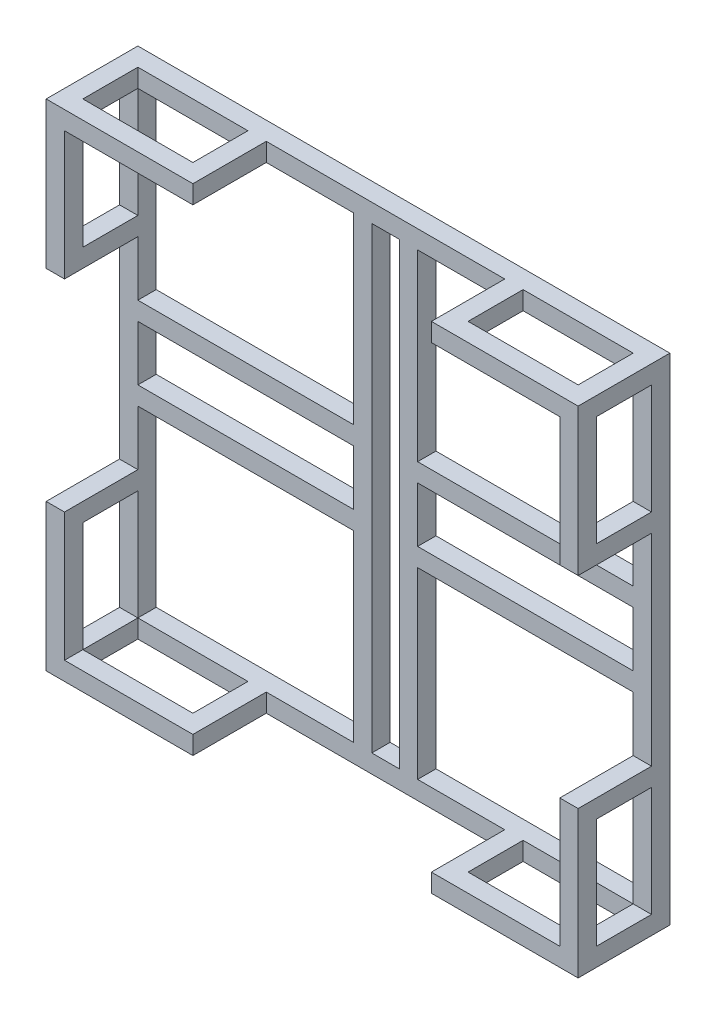
SolidWorks part; units mm, degrees
ref_plane "前视基准面" through (0, 0, 0) normal (0, 0, 1) x (1, 0, 0)
ref_plane "上视基准面" through (0, 0, 0) normal (0, 1, 0) x (1, 0, 0)
ref_plane "右视基准面" through (0, 0, 0) normal (1, 0, 0) x (0, 0, -1)
sketch "草图1" plane through (0, 0, 0) normal (0, 0, 1) x (1, 0, 0)
  line L1 (0, 0) -> (580, 0)
  line L2 (0, 0) -> (0, 540)
  line L3 (0, 540) -> (580, 540)
  line L4 (580, 0) -> (580, 540)
  dimension "D1" = 580
  dimension "D2" = 540
extrude "凸台-拉伸1" add sketch "草图1" along normal blind 100 contours L3 L4 L1 L2
shell "抽壳1" thickness 20
sketch "草图2" plane through (0, 0, 20) normal (0, 0, 1) x (1, 0, 0)
  line L1 (560, 20) -> (325, 20)
  line L2 (560, 20) -> (560, 220)
  line L3 (560, 220) -> (325, 220)
  line L4 (325, 20) -> (325, 220)
  dimension "D1" = 235
  dimension "D2" = 200
extrude "切除-拉伸1" cut sketch "草图2" against normal blind 43 contours L3 L4 L1 L2
pattern_linear "阵列(线性)1" count 2 spacing 305 along (-1, 0, 0) of "切除-拉伸1"
pattern_linear "阵列(线性)2" count 2 spacing 300 along (0, 1, 0) of "切除-拉伸1"
pattern_linear "阵列(线性)3" count 2 spacing 300 along (0, 1, 0) of "阵列(线性)1"
sketch "草图3" plane through (0, 0, 0) normal (0, -1, 0) x (1, 0, 0)
  line L0 (580, 100) -> (420, 100) construction
  line L1 (0, 100) -> (580, 100) construction
  line L2 (0, 100) -> (160, 100) construction
  line L3 (160, 100) -> (160, 20) construction
  line L4 (420, 100) -> (420, 20) construction
  dimension "D1" = 160
  dimension "D2" = 160
  dimension "D3" = 80
  dimension "D4" = 80
sketch "草图4" plane through (0, 0, 0) normal (0, -1, 0) x (1, 0, 0)
  line L1 (160, 100) -> (420, 100)
  line L2 (160, 100) -> (160, 20)
  line L3 (160, 20) -> (420, 20)
  line L4 (420, 100) -> (420, 20)
extrude "切除-拉伸2" cut sketch "草图4" against normal blind 549 contours L3 L4 L1 L2
sketch "草图5" plane through (580, 0, 0) normal (1, 0, 0) x (0, 0, -1)
  line L0 (-100, 540) -> (-100, 380) construction
  line L1 (-100, 0) -> (-100, 540) construction
  line L2 (-100, 0) -> (-100, 160) construction
  line L3 (-100, 160) -> (-20, 160) construction
  line L4 (-100, 380) -> (-20, 380) construction
  dimension "D1" = 160
  dimension "D2" = 160
  dimension "D3" = 80
sketch "草图6" plane through (580, 0, 0) normal (1, 0, 0) x (0, 0, -1)
  line L1 (-100, 380) -> (-20, 380)
  line L2 (-100, 380) -> (-100, 160)
  line L3 (-100, 160) -> (-20, 160)
  line L4 (-20, 380) -> (-20, 160)
extrude "切除-拉伸3" cut sketch "草图6" against normal blind 614 contours L4 L3 L2 L1
sketch "草图7" plane through (0, 0, 0) normal (0, -1, 0) x (1, 0, 0)
  line L0 (160, 20) -> (140, 20) construction
  dimension "D1" = 20
sketch "草图8" plane through (0, 0, 0) normal (0, -1, 0) x (1, 0, 0)
  line L1 (140, 20) -> (20, 20)
  line L2 (140, 20) -> (140, 80)
  line L3 (140, 80) -> (20, 80)
  line L4 (20, 20) -> (20, 80)
  dimension "D1" = 60
  dimension "D2" = 120
extrude "切除-拉伸4" cut sketch "草图8" against normal blind 614 contours L3 L4 L1 L2
sketch "草图9" plane through (0, 0, 0) normal (0, -1, 0) x (1, 0, 0)
  line L0 (420, 20) -> (440, 20) construction
  dimension "D1" = 20
sketch "草图10" plane through (0, 0, 0) normal (0, -1, 0) x (1, 0, 0)
  line L1 (440, 20) -> (560, 20)
  line L2 (440, 20) -> (440, 80)
  line L3 (440, 80) -> (560, 80)
  line L4 (560, 20) -> (560, 80)
  dimension "D1" = 120
  dimension "D2" = 60
extrude "切除-拉伸5" cut sketch "草图10" against normal blind 614 contours L3 L4 L1 L2
sketch "草图11" plane through (580, 0, 0) normal (1, 0, 0) x (0, 0, -1)
  line L0 (-100, 380) -> (-100, 400) construction
  line L1 (-100, 540) -> (-100, 380) construction
  line L2 (-100, 400) -> (-80, 400) construction
  dimension "D1" = 20
  dimension "D2" = 20
sketch "草图12" plane through (580, 0, 0) normal (1, 0, 0) x (0, 0, -1)
  line L1 (-80, 400) -> (-20, 400)
  line L2 (-80, 400) -> (-80, 520)
  line L3 (-80, 520) -> (-20, 520)
  line L4 (-20, 400) -> (-20, 520)
  dimension "D1" = 60
  dimension "D2" = 120
extrude "切除-拉伸6" cut sketch "草图12" against normal blind 602 contours L3 L4 L1 L2
sketch "草图13" plane through (580, 0, 0) normal (1, 0, 0) x (0, 0, -1)
  line L0 (-100, 160) -> (-100, 140) construction
  line L1 (-100, 0) -> (-100, 160) construction
  line L2 (-100, 140) -> (-80, 140) construction
  line L4 (-80, 140) -> (-20, 140)
  line L5 (-80, 140) -> (-80, 20)
  line L6 (-80, 20) -> (-20, 20)
  line L7 (-20, 140) -> (-20, 20)
  dimension "D1" = 20
  dimension "D2" = 20
  dimension "D3" = 120
  dimension "D4" = 60
extrude "切除-拉伸7" cut sketch "草图13" against normal blind 602 contours L4 L7 L6 L5
sketch "草图14" plane through (0, 0, 20) normal (0, 0, 1) x (1, 0, 0)
  line L0 (255, 520) -> (275, 520) construction
  line L1 (325, 520) -> (305, 520) construction
  line L3 (255, 20) -> (275, 20) construction
  line L4 (325, 20) -> (305, 20) construction
  dimension "D1" = 20
  dimension "D2" = 20
sketch "草图15" plane through (0, 0, 20) normal (0, 0, 1) x (1, 0, 0)
  line L1 (275, 520) -> (305, 520)
  line L2 (275, 520) -> (275, 20)
  line L3 (275, 20) -> (305, 20)
  line L4 (305, 520) -> (305, 20)
extrude "切除-拉伸8" cut sketch "草图15" against normal blind 66 contours L4 L3 L2 L1
sketch "草图16" plane through (0, 0, 20) normal (0, 0, 1) x (1, 0, 0)
  line L0 (20, 320) -> (20, 300) construction
  line L1 (20, 220) -> (20, 240) construction
  line L2 (560, 320) -> (560, 300) construction
  line L3 (560, 220) -> (560, 240) construction
  line L4 (255, 320) -> (255, 300) construction
  line L5 (325, 320) -> (325, 300) construction
  dimension "D1" = 20
  dimension "D2" = 20
  dimension "D3" = 20
  dimension "D4" = 20
  dimension "D5" = 20
  dimension "D6" = 20
sketch "草图18" plane through (0, 0, 20) normal (0, 0, 1) x (1, 0, 0)
  line L1 (20, 240) -> (255, 240)
  line L2 (20, 240) -> (20, 300)
  line L3 (20, 300) -> (255, 300)
  line L4 (255, 240) -> (255, 300)
extrude "切除-拉伸11" cut sketch "草图18" against normal blind 41 contours L3 L4 L1 L2
sketch "草图19" plane through (0, 0, 20) normal (0, 0, 1) x (1, 0, 0)
  line L0 (325, 320) -> (325, 300) construction
  dimension "D1" = 20
sketch "草图20" plane through (0, 0, 20) normal (0, 0, 1) x (1, 0, 0)
sketch "草图21" plane through (0, 0, 20) normal (0, 0, 1) x (1, 0, 0)
  line L1 (325, 300) -> (560, 300)
  line L2 (325, 300) -> (325, 240)
  line L3 (325, 240) -> (560, 240)
  line L4 (560, 300) -> (560, 240)
extrude "切除-拉伸13" cut sketch "草图21" against normal blind 72 contours L1 L4 L3 L2
